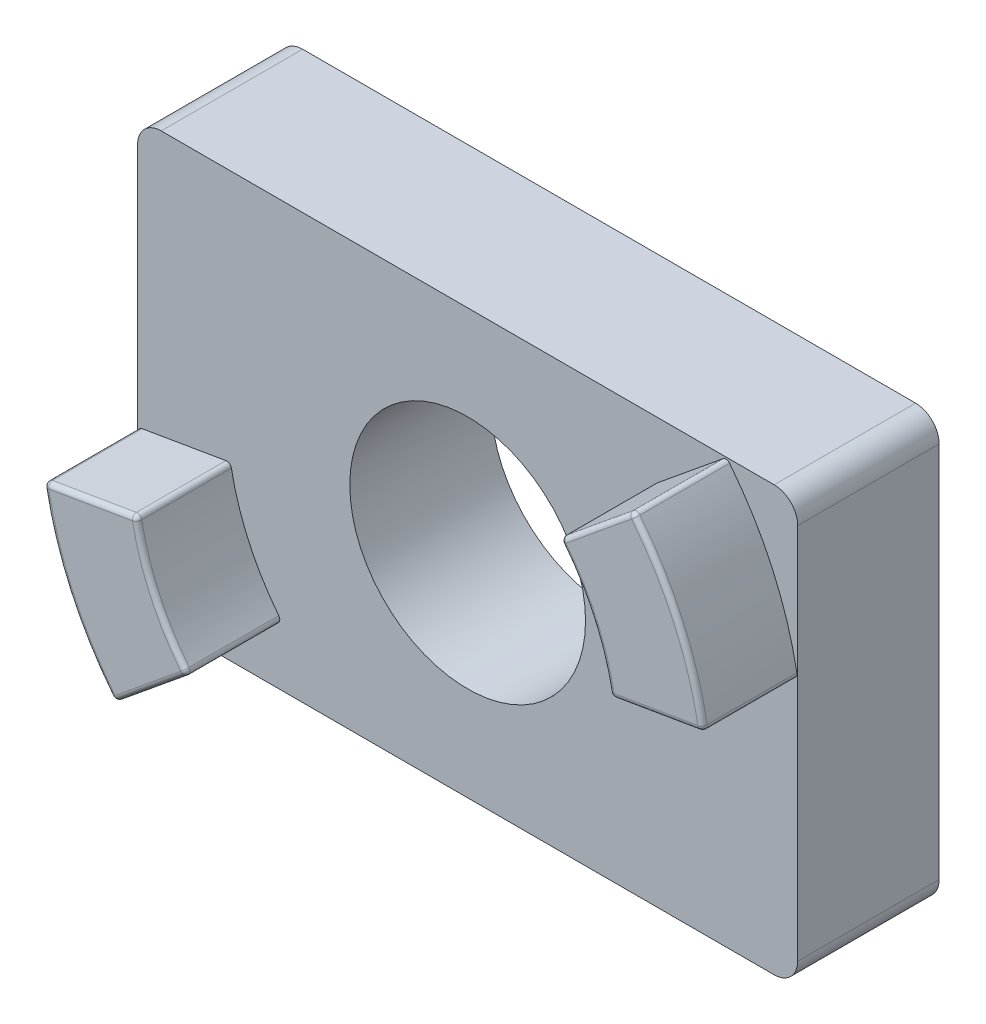
SolidWorks part; units mm, degrees
ref_plane "Front Plane" through (0, 0, 0) normal (0, 0, 1) x (1, 0, 0)
ref_plane "Top Plane" through (0, 0, 0) normal (0, 1, 0) x (1, 0, 0)
ref_plane "Right Plane" through (0, 0, 0) normal (1, 0, 0) x (0, 0, -1)
sketch "Sketch1" plane through (0, 0, 0) normal (0, 0, 1) x (1, 0, 0)
  line L1 (-7, 4.5) -> (7, 4.5)
  line L2 (-7, 4.5) -> (-7, -4.5)
  line L3 (-7, -4.5) -> (7, -4.5)
  line L4 (7, 4.5) -> (7, -4.5)
  circle A0 centre (0, 0) radius 2.5
  point P7 (-7, 0)
  point P8 (0, 4.5)
  dimension "D1" = 5
  dimension "D2" = 9
  dimension "D3" = 14
extrude "Boss-Extrude1" add sketch "Sketch1" along normal blind 3
fillet "Fillet1" radius 0.5 4 edges at (7, -4.5, 1.5) (-7, -4.5, 1.5) (7, 4.5, 1.5) (-7, 4.5, 1.5)
sketch "Sketch2" plane through (0, 0, 3) normal (0, 0, 1) x (1, 0, 0)
  line L1 (0, 0) -> (5.4918, 4.5) construction
  line L2 (6.5, 4.5) -> (-6.5, 4.5) construction
  line L3 (0, 0) -> (7, 1.1874) construction
  line L4 (7, -4) -> (7, 4) construction
  line L5 (0, 0) -> (-5.4918, -4.5) construction
  line L6 (-6.5, -4.5) -> (6.5, -4.5) construction
  line L7 (0, 0) -> (-7, -1.1874) construction
  line L8 (-7, 4) -> (-7, -4) construction
  line L9 (5.4918, 4.5) -> (3.9448, 3.2324)
  line L10 (7, 1.1874) -> (5.0282, 0.8529)
  line L11 (-5.0282, -0.8529) -> (-7, -1.1874)
  line L12 (-5.4918, -4.5) -> (-3.9448, -3.2324)
  circle A0 centre (0, 0) radius 5.1 construction
  circle A1 centre (0, 0) radius 7.1 construction
  arc A2 (-5.0282, -0.8529) -> (-3.9448, -3.2324) centre (0, 0) ccw
  arc A3 (-7, -1.1874) -> (-5.4918, -4.5) centre (0, 0) ccw
  arc A4 (5.4918, 4.5) -> (7, 1.1874) centre (0, 0) cw
  arc A5 (3.9448, 3.2324) -> (5.0282, 0.8529) centre (0, 0) cw
  dimension "D1" = 10.2
  dimension "D2" = 2
extrude "Boss-Extrude2" add sketch "Sketch2" along normal blind 2 contours L11 A3 L12 A2 | L9 A5 L10 A4
fillet "Fillet2" radius 0.1 16 edges at (5.4918, 4.5, 4) (7, 1.1874, 4) (6.4618, 2.942, 5) (4.7183, 3.8662, 5) (3.9448, 3.2324, 4) (4.6416, 2.1133, 5) (6.0141, 1.0202, 5) (5.0282, 0.8529, 4) (-7, -1.1874, 4) (-5.0282, -0.8529, 4) (-3.9448, -3.2324, 4) (-4.6416, -2.1133, 5) (-6.0141, -1.0202, 5) (-6.4618, -2.942, 5) (-5.4918, -4.5, 4) (-4.7183, -3.8662, 5)
